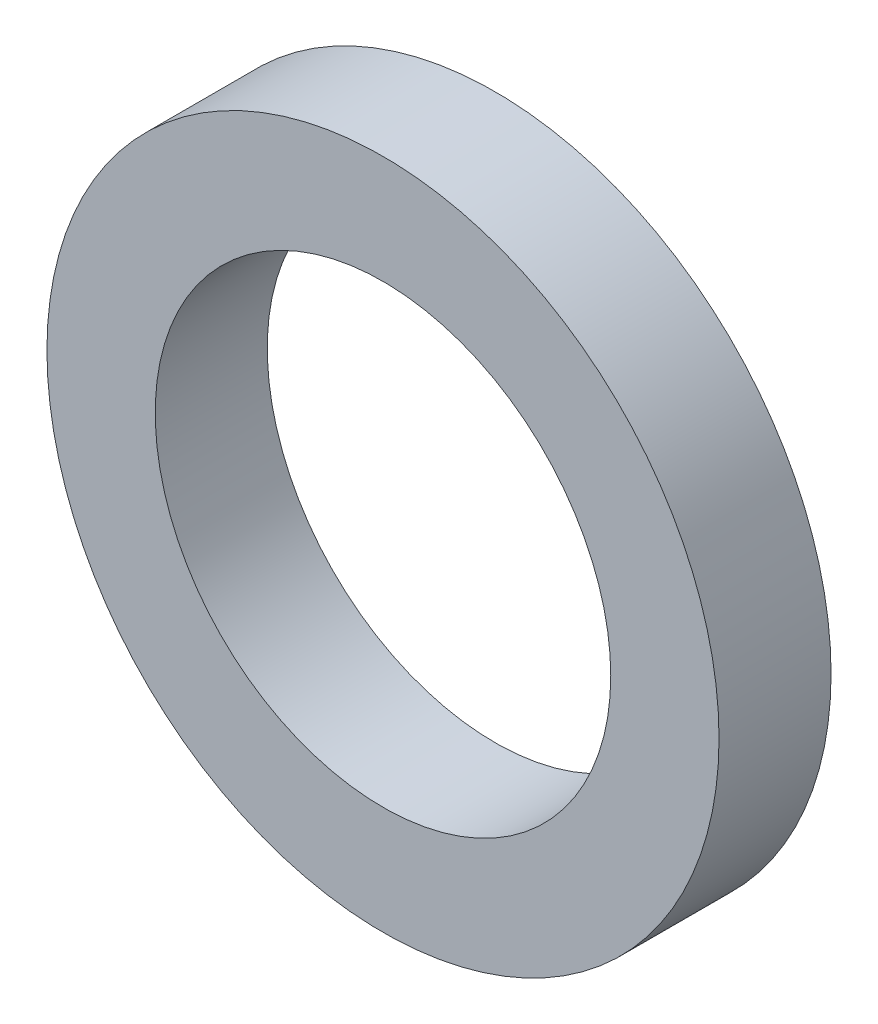
SolidWorks part; units mm, degrees
ref_plane "前视基准面" through (0, 0, 0) normal (0, 0, 1) x (1, 0, 0)
ref_plane "上视基准面" through (0, 0, 0) normal (0, 1, 0) x (1, 0, 0)
ref_plane "右视基准面" through (0, 0, 0) normal (1, 0, 0) x (0, 0, -1)
sketch "草图1" plane through (0, 0, 0) normal (0, 0, 1) x (1, 0, 0)
  circle A0 centre (0, 0) radius 4.5
  dimension "D1" = 9
extrude "凸台-拉伸1" add sketch "草图1" along normal blind 1.5
sketch "草图2" plane through (0, 0, 1.5) normal (0, 0, 1) x (1, 0, 0)
  circle A0 centre (0, 0) radius 3.05
  dimension "D1" = 6.1
extrude "切除-拉伸1" cut sketch "草图2" against normal through all
